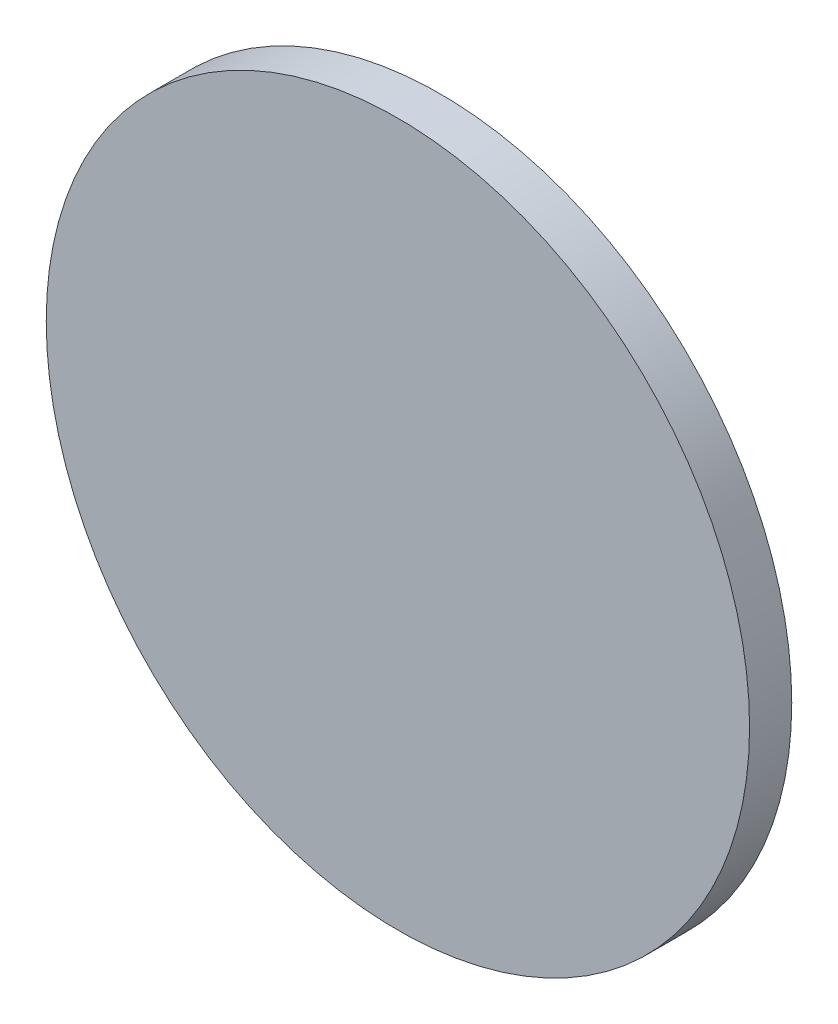
SolidWorks part; units mm, degrees
ref_plane "前视基准面" through (0, 0, 0) normal (0, 0, 1) x (1, 0, 0)
ref_plane "上视基准面" through (0, 0, 0) normal (0, 1, 0) x (1, 0, 0)
ref_plane "右视基准面" through (0, 0, 0) normal (1, 0, 0) x (0, 0, -1)
sketch "草图1" plane through (0, 0, 0) normal (0, 0, 1) x (1, 0, 0)
  circle A0 centre (0, 0) radius 25
  dimension "D1" = 50
extrude "凸台-拉伸1" add sketch "草图1" along normal blind 3
